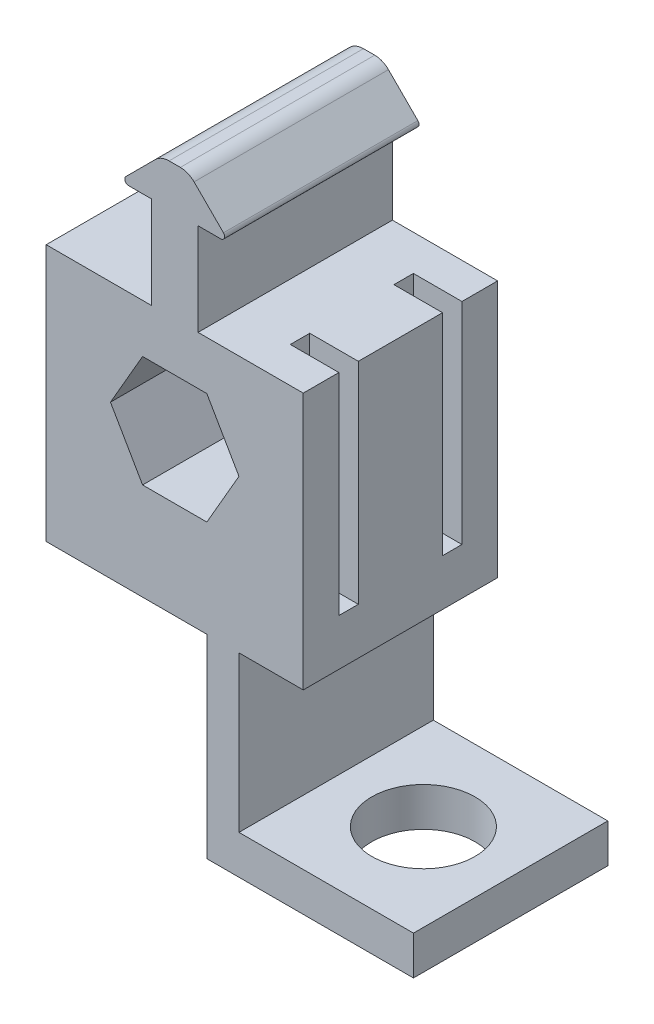
SolidWorks part; units mm, degrees
ref_plane "Front Plane" through (0, 0, 0) normal (0, 0, 1) x (1, 0, 0)
ref_plane "Top Plane" through (0, 0, 0) normal (0, 1, 0) x (1, 0, 0)
ref_plane "Right Plane" through (0, 0, 0) normal (1, 0, 0) x (0, 0, -1)
sketch "Sketch1" plane through (0, 0, 0) normal (0, 0, 1) x (1, 0, 0)
  line L0 (-16.7958, 13.6208) -> (-16.7957, -19.9708)
  line L1 (-4.1978, 7.2708) -> (-8.3955, 0)
  line L2 (-8.3955, 0) -> (-4.1978, -7.2707)
  line L3 (-4.1978, -7.2707) -> (4.1978, -7.2707)
  line L4 (4.1978, -7.2707) -> (8.3955, 0)
  line L5 (8.3955, 0) -> (4.1978, 7.2708)
  line L6 (4.1978, 7.2708) -> (-4.1978, 7.2708)
  line L7 (-16.7957, -19.9708) -> (16.7958, -19.9707)
  line L8 (16.7958, -19.9707) -> (16.7958, 13.6208)
  line L9 (-16.7958, 13.6208) -> (-3.048, 13.6208)
  line L10 (-3.048, 13.6208) -> (-3.048, 25.6857)
  line L11 (-3.048, 25.6857) -> (-6.0126, 25.6857)
  line L12 (-6.3718, 26.553) -> (-2.5321, 30.3926)
  line L13 (-0.7361, 31.1366) -> (0.7361, 31.1366)
  line L14 (0, 41.8096) -> (0, -25.778) construction
  line L15 (16.7958, 13.6208) -> (3.048, 13.6207)
  line L16 (3.048, 13.6207) -> (3.048, 25.6857)
  line L17 (6.3718, 26.553) -> (2.5321, 30.3926)
  line L18 (3.048, 25.6857) -> (6.0126, 25.6857)
  circle A0 centre (0, 0) radius 7.2707 construction
  arc A1 (-6.0126, 25.6857) -> (-6.3718, 26.553) centre (-6.0126, 26.1938) cw
  arc A2 (-2.5321, 30.3926) -> (-0.7361, 31.1366) centre (-0.7361, 28.5966) cw
  arc A3 (2.5321, 30.3926) -> (0.7361, 31.1366) centre (0.7361, 28.5966) ccw
  arc A4 (6.0126, 25.6857) -> (6.3718, 26.553) centre (6.0126, 26.1938) ccw
  point P18 (7.239, 25.6857)
  point P21 (-4.5303, 25.6857)
  point P25 (-7.239, 25.6857)
  point P29 (0, -19.9708)
  point P35 (0, 31.1366)
  dimension "D7" = 0.508
  dimension "D8" = 2.54
  dimension "D1" = 14.5415
  dimension "D2" = 18.415
  dimension "D3" = 6.096
  dimension "D4" = 5.4508
  dimension "D5" = 135
  dimension "D6" = 14.478
  dimension "D9" = 12.7
  dimension "D10" = 6.35
extrude "Boss-Extrude1" add sketch "Sketch1" along normal mid plane 25.4
sketch "Sketch8" plane through (16.7958, 0, 0) normal (1, 0, 0) x (0, 0, -1)
  line L0 (-12.7, 13.6208) -> (12.7, 13.6208) construction
  line L1 (-8.04, 13.6208) -> (-5.5, 13.6208)
  line L2 (-8.04, 13.6208) -> (-8.04, -13.8792)
  line L3 (-8.04, -13.8792) -> (-5.5, -13.8792)
  line L4 (-5.5, 13.6208) -> (-5.5, -13.8792)
  line L5 (5.5, 13.6208) -> (5.5, -13.8792)
  line L10 (0, 20.1653) -> (0, -17.7306) construction
  line L11 (8.04, -13.8792) -> (5.5, -13.8792)
  line L12 (8.04, 13.6208) -> (8.04, -13.8792)
  line L13 (8.04, 13.6208) -> (5.5, 13.6208)
  dimension "D1" = 11
  dimension "D2" = 2.54
  dimension "D3" = 27.5
extrude "Cut-Extrude1" cut sketch "Sketch8" against normal blind 6.35
sketch "Sketch3" plane through (0, -19.9708, 0) normal (0, -1, 0) x (1, 0, 0)
  line L0 (8.3955, 12.7) -> (8.3955, -12.7) construction
  line L3 (8.3955, 12.7) -> (8.3955, -12.7)
  line L7 (4.1978, 12.7) -> (4.1978, -12.7) construction
  line L8 (4.1978, 12.7) -> (4.1978, -12.7)
  line L9 (4.1978, 12.7) -> (8.3955, 12.7)
  line L10 (4.1978, -12.7) -> (8.3955, -12.7)
extrude "Boss-Extrude2" add sketch "Sketch3" along normal blind 25.4
sketch "Sketch4" plane through (0, -45.3708, 0) normal (0, -1, 0) x (1, 0, 0)
  line L2 (8.3955, 12.7) -> (31.196, 12.7)
  line L3 (31.196, 12.7) -> (31.196, -12.7)
  line L4 (31.196, -12.7) -> (8.3955, -12.7)
  line L8 (8.3955, -12.7) -> (8.3955, 12.7) construction
  line L9 (8.3955, -12.7) -> (8.3955, 12.7)
  line L10 (16.7958, 12.7) -> (16.7958, -12.7) construction
  line L11 (16.7958, 12.7) -> (16.7958, -12.7) construction
  circle A0 centre (19.7958, 0) radius 6.75
  point P7 (19.7958, 12.7)
  dimension "D1" = 13.5
  dimension "D2" = 3
extrude "Boss-Extrude3" add sketch "Sketch4" against normal blind 5.08
